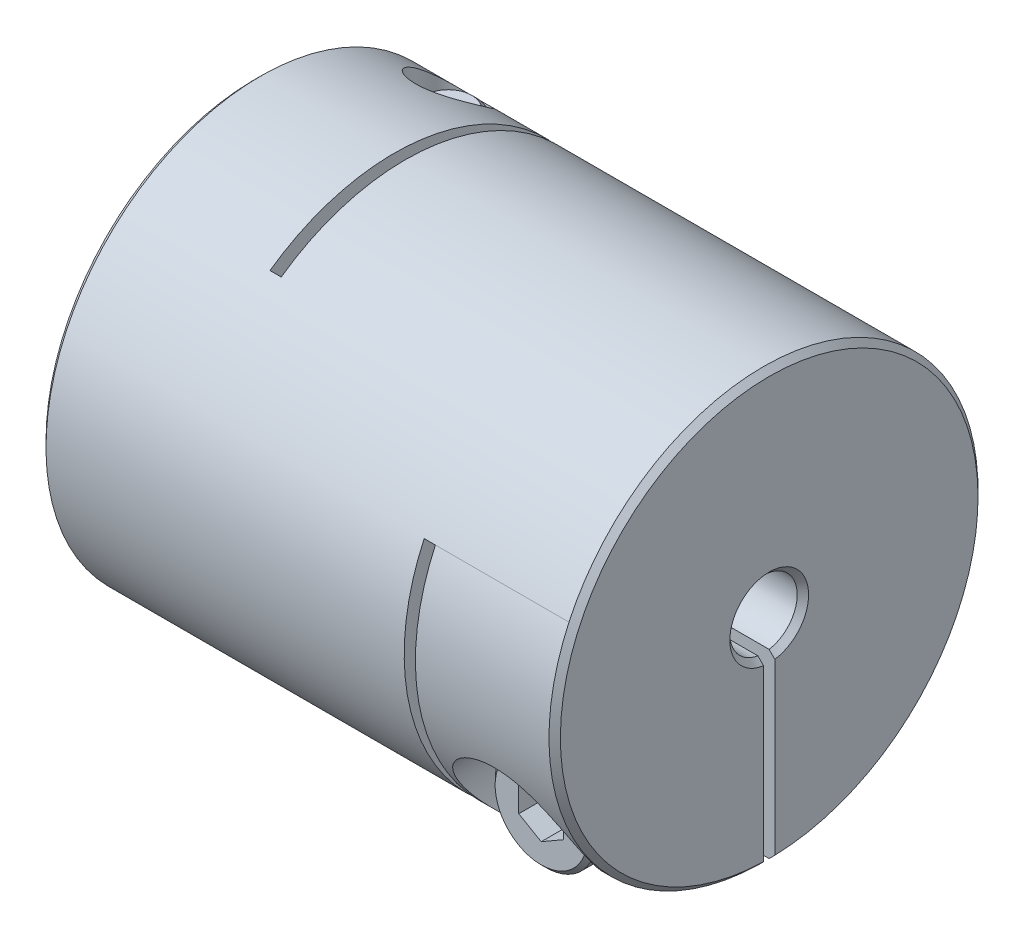
SolidWorks part; units mm, degrees
ref_plane "Front Plane" through (0, 0, 0) normal (0, 0, 1) x (1, 0, 0)
ref_plane "Top Plane" through (0, 0, 0) normal (0, 1, 0) x (1, 0, 0)
ref_plane "Right Plane" through (0, 0, 0) normal (1, 0, 0) x (0, 0, -1)
sketch "Sketch1" plane through (0, 0, 0) normal (1, 0, 0) x (0, 0, -1)
  circle A0 centre (0, 0) radius 9.55
  dimension "dim D" = 19.1
extrude "Boss-Extrude1" add sketch "Sketch1" along normal mid plane 22.9
sketch "Sketch2" plane through (11.45, 0, 0) normal (1, 0, 0) x (0, 0, -1)
  circle A0 centre (0, 0) radius 1.5
  dimension "dim D1" = 3
extrude "Cut-Extrude1" cut sketch "Sketch2" against normal through all
chamfer "Chamfer1" distance 0.254 angle 45 4 edges at (-11.45, 0, -1.5) (-11.45, 0, -9.55) (11.45, 0, -9.55) (11.45, 0, -1.5)
ref_plane "Plane2" through (0, -9.55, 0) normal (0, -1, 0) x (1, 0, 0)
ref_plane "L1" through (-8.35, 0, 0) normal (-1, 0, 0) x (0, 0, 1)
sketch "Sketch4" plane through (0, -9.55, 0) normal (0, -1, 0) x (1, 0, 0)
  line L0 (-11.196, -9.55) -> (11.196, -9.55) construction
  line L1 (-5.25, -9.55) -> (-4.75, -9.55)
  line L2 (-5.25, -9.55) -> (-5.25, 5.525)
  line L3 (-5.25, 5.525) -> (-4.75, 5.525)
  line L4 (-4.75, -9.55) -> (-4.75, 5.525)
  line L5 (-5.25, 1.5) -> (-5.25, 9.55) construction
  line L6 (11.196, 1.5) -> (-11.196, 1.5) construction
  line L7 (11.196, 9.55) -> (-11.196, 9.55) construction
  line L10 (-5.25, 5.525) -> (-11.45, 5.525) construction
  line L11 (-11.45, 9.296) -> (-11.45, -9.296) construction
  line L12 (-8.35, 10.2256) -> (-8.35, -10.2256) construction
  point P16 (-8.35, 5.525)
  dimension "D1" = 0.5
extrude "Cut-Extrude2" cut sketch "Sketch4" against normal through all
ref_plane "Plane4" through (0, 0, -9.55) normal (0, 0, -1) x (-1, 0, 0)
sketch "Sketch7" plane through (0, 0, -9.55) normal (0, 0, -1) x (-1, 0, 0)
  line L1 (-4.75, -9.55) -> (-5.25, -9.55)
  line L2 (-5.25, -9.55) -> (-5.25, 4.025)
  line L3 (-5.25, 4.025) -> (-4.75, 4.025)
  line L4 (-4.75, -9.55) -> (-4.75, 4.025)
  line L5 (11.45, 8.6487) -> (8.35, 8.6487) construction
  line L7 (-10.505, -9.55) -> (10.505, -9.55) construction
  line L8 (-11.196, -1.5) -> (4.75, -1.5) construction
  line L9 (11.45, -9.296) -> (11.45, 9.296) construction
  line L10 (-11.196, -1.5) -> (4.75, -1.5) construction
  line L11 (4.75, 7.7895) -> (5.25, 7.7895) construction
  line L12 (-5.25, 4.025) -> (-5.25, -9.55) construction
  line L14 (-11.196, -1.5) -> (4.75, -1.5) construction
  line L16 (-11.196, -1.5) -> (4.75, -1.5) construction
  line L17 (5.25, -9.55) -> (11.196, -9.55) construction
  line L18 (8.35, -10.2256) -> (8.35, 10.2256) construction
  line L19 (-11.196, -9.55) -> (-11.196, 9.55) construction
  line L20 (-11.45, 4.025) -> (-8.35, 4.025) construction
  line L21 (-11.45, 9.296) -> (-11.45, -9.296) construction
  line L22 (-8.35, 4.025) -> (-5.25, 4.025) construction
  line L23 (-11.196, -9.55) -> (-11.196, 9.55) construction
  line L24 (-11.196, -1.5) -> (-11.196, 9.55) construction
  line L25 (-11.196, -1.5) -> (4.75, -1.5) construction
  point P23 (-5.25, 4.025)
  point P33 (-11.196, 4.025)
extrude "Cut-Extrude3" cut sketch "Sketch7" against normal through all
sketch "Sketch8" plane through (0, 0, 0) normal (0, 1, 0) x (1, 0, 0)
  line L0 (-5.25, -5.525) -> (-5.25, 9.55) construction
  line L1 (-11.45, 9.55) -> (-5.25, 9.55)
  line L2 (-11.45, 9.55) -> (-11.45, 0)
  line L3 (-11.45, 0) -> (-5.25, 0)
  line L4 (-5.25, 9.55) -> (-5.25, 0)
  line L5 (10.505, 9.55) -> (-10.505, 9.55) construction
  line L6 (-11.45, 9.296) -> (-11.45, -9.296) construction
extrude "Cut-Extrude5" cut sketch "Sketch8" against normal mid plane 0.5
sketch "Sketch13" plane through (0, 0, 0) normal (0, 0, 1) x (1, 0, 0)
  line L0 (11.45, -9.296) -> (11.45, 9.296) construction
  line L1 (5.25, -9.55) -> (11.45, -9.55)
  line L2 (5.25, -9.55) -> (5.25, 0)
  line L3 (5.25, 0) -> (11.45, 0)
  line L4 (11.45, -9.55) -> (11.45, 0)
extrude "Cut-Extrude6" cut sketch "Sketch13" against normal mid plane 0.5
hole_wizard "CBORE for M2.5 SHCS1" positions "Sketch12" profile "Sketch11" counterbore size "M2.5" standard "Ansi Metric" end condition through all
sketch "Sketch12" plane through (0, -9.55, 0) normal (0, -1, 0) x (1, 0, 0)
  line L0 (-8.35, 10.2256) -> (-8.35, -10.2256) construction
  line L1 (-5.25, -1.479) -> (-5.25, -9.5467) construction
  line L2 (-5.25, -1.479) -> (-5.25, -9.5467)
  line L3 (-5.25, -5.5129) -> (-8.35, -5.5129) construction
  point P0 (-8.35, -5.5129)
sketch "Sketch11" plane through (-8.35, -9.55, -5.5129) normal (1, 0, 0) x (0, 0, -1)
  line L0 (0, 0) -> (0, 19.1)
  line L1 (0, 19.1) -> (1.45, 19.1)
  line L3 (1.45, 19.1) -> (1.45, 5)
  line L4 (1.45, 5) -> (2.75, 5)
  line L5 (2.75, 5) -> (2.75, 0)
  line L7 (2.75, 0) -> (0, 0)
  line L11 (0, -6.35) -> (0, 107.95) construction
  dimension "Thru Hole Dia." = 2.9
  dimension "Thru Hole Depth" = 19.1
  dimension "C'Bore Dia." = 5.5
  dimension "C'Bore Depth" = 5
ref_plane "Plane5" through (0, 0, 9.55) normal (0, 0, 1) x (1, 0, 0)
hole_wizard "CBORE for M2.5 SHCS2" positions "Sketch15" profile "Sketch14" counterbore size "M2.5" standard "Ansi Metric" end condition through all
sketch "Sketch15" plane through (0, 0, 9.55) normal (0, 0, 1) x (1, 0, 0)
  line L0 (-11.1, -4.55) -> (-5.6, -4.55) construction
  line L1 (-11.1, -4.55) -> (-5.6, -4.55)
  line L5 (0, 0) -> (0, 9.55) construction
  line L6 (-5.25, 9.55) -> (-11.196, 9.55) construction
  line L8 (11.1, -4.55) -> (5.6, -4.55)
  line L9 (8.35, -4.55) -> (8.35, -5.5129) construction
  line L11 (8.35, -9.5467) -> (8.35, -1.479) construction
  line L12 (11.196, -9.5467) -> (5.25, -9.5467) construction
  line L13 (5.25, -1.479) -> (11.196, -1.479) construction
  point P0 (8.35, -5.5129)
sketch "Sketch14" plane through (8.35, -5.5129, 9.55) normal (1, 0, 0) x (0, -1, 0)
  line L0 (0, 0) -> (0, 19.1)
  line L1 (0, 19.1) -> (1.45, 19.1)
  line L3 (1.45, 19.1) -> (1.45, 5)
  line L4 (1.45, 5) -> (2.75, 5)
  line L5 (2.75, 5) -> (2.75, 0)
  line L7 (2.75, 0) -> (0, 0)
  line L11 (0, -6.35) -> (0, 107.95) construction
  dimension "Thru Hole Dia." = 2.9
  dimension "Thru Hole Depth" = 19.1
  dimension "C'Bore Dia." = 5.5
  dimension "C'Bore Depth" = 5
sketch "Sketch16" plane through (0, 0, 4.55) normal (0, 0, 1) x (1, 0, 0)
  circle A0 centre (8.35, -5.5129) radius 2.25
  dimension "screw dia" = 4.5
extrude "Boss-Extrude2" add sketch "Sketch16" along normal blind 2.5 separate body
sketch "Sketch17" plane through (0, 0, 4.55) normal (0, 0, -1) x (-1, 0, 0)
  circle A0 centre (-8.35, -5.5129) radius 1.25
  dimension "D1" = 2.5
extrude "Boss-Extrude3" add sketch "Sketch17" along normal blind 11.5
chamfer "Chamfer2" distance 0.2 angle 45 3 edges at (7.1, -5.5129, -6.95) (10.6, -5.5129, 4.55) (10.6, -5.5129, 7.05)
sketch "Sketch18" plane through (0, 0, 7.05) normal (0, 0, 1) x (1, 0, 0)
  line L1 (8.35, -6.6676) -> (9.35, -6.0902)
  line L2 (9.35, -6.0902) -> (9.35, -4.9355)
  line L3 (9.35, -4.9355) -> (8.35, -4.3582)
  line L4 (8.35, -4.3582) -> (7.35, -4.9355)
  line L5 (7.35, -4.9355) -> (7.35, -6.0902)
  line L6 (7.35, -6.0902) -> (8.35, -6.6676)
  circle A0 centre (8.35, -5.5129) radius 1 construction
  dimension "hex" = 2
extrude "Cut-Extrude7" cut sketch "Sketch18" against normal blind 1.5
mirror "Mirror1" about plane through (0, 0, 0) normal (1, 0, 0) of bodies 121
pattern_circular "CirPattern1" count 2 every 90 about axis through (0, 0, 0) along (1, 0, 0) of bodies 122
delete or keep bodies "Body-Delete1" type delete bodies bodies 122
